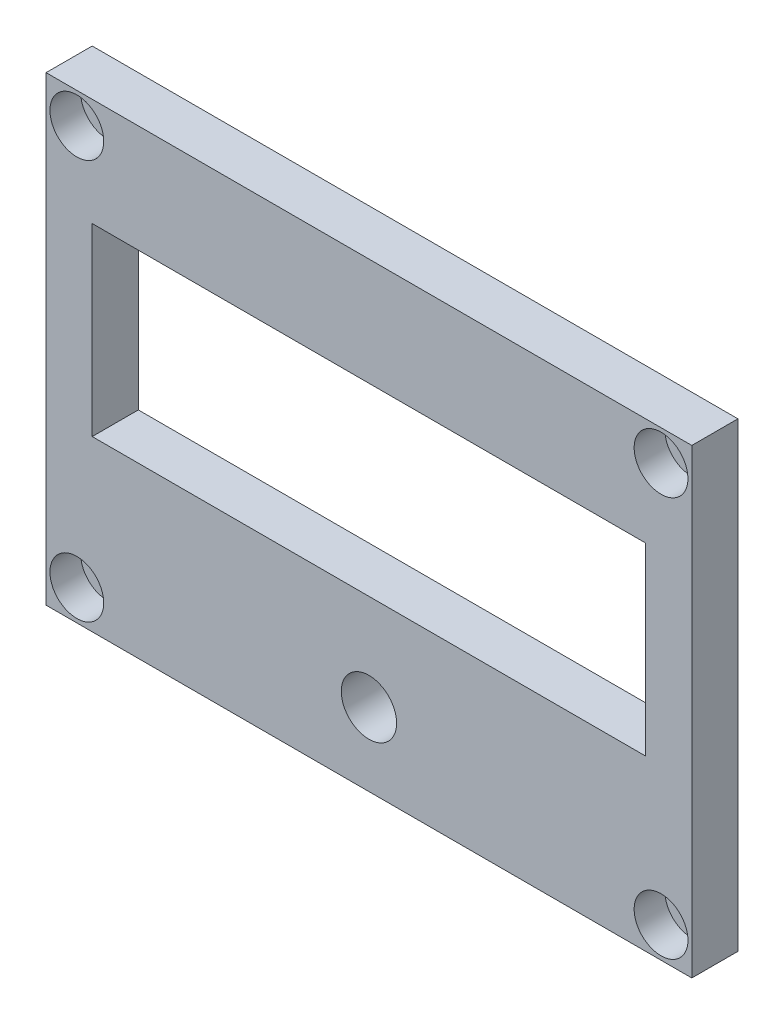
SolidWorks part; units mm, degrees
ref_plane "Front Plane" through (0, 0, 0) normal (0, 0, 1) x (1, 0, 0)
ref_plane "Top Plane" through (0, 0, 0) normal (0, 1, 0) x (1, 0, 0)
ref_plane "Right Plane" through (0, 0, 0) normal (1, 0, 0) x (0, 0, -1)
sketch "Sketch1" plane through (0, 0, 0) normal (0, 0, 1) x (1, 0, 0)
  line L0 (-37, 30) -> (-40, 30)
  line L1 (-37, -30) -> (37, -30)
  line L2 (-40, -27) -> (-40, 27)
  line L3 (-37, 30) -> (37, 30)
  line L4 (44, -27) -> (44, 27)
  line L6 (-37, -30) -> (-40, -30)
  line L7 (-40, 30) -> (-40, 27)
  line L8 (44, -27) -> (44, -30)
  line L9 (37, 30) -> (44, 30)
  line L10 (44, 30) -> (44, 27)
  line L11 (44, -30) -> (37, -30)
  line L12 (-40, -30) -> (-40, -27)
  point P0 (0, 0)
  dimension "D1" = 84
  dimension "D2" = 60
extrude "Boss-Extrude1" add sketch "Sketch1" along normal blind 6
sketch "Sketch3" plane through (0, 0, 6) normal (0, 0, 1) x (1, 0, 0)
  circle A4 centre (-36, 26) radius 3.5
  circle A5 centre (40, 26) radius 3.5
  circle A6 centre (40, -26) radius 3.5
  circle A7 centre (-36, -26) radius 3.5
extrude "Cut-Extrude2" cut sketch "Sketch3" against normal blind 4
sketch "Sketch4" plane through (0, 0, 6) normal (0, 0, 1) x (1, 0, 0)
  circle A0 centre (-36, 26) radius 2
  circle A1 centre (40, 26) radius 2
  circle A2 centre (40, -26) radius 2
  circle A3 centre (-36, -26) radius 2
extrude "Cut-Extrude3" cut sketch "Sketch4" against normal up to surface (6 mm away) up to face at (2, 0, 0)
sketch "Sketch6" plane through (0, 0, 0) normal (0, 0, -1) x (-1, 0, 0)
  line L10 (30.5, -8) -> (-34.5, -8)
  line L14 (-2, 16) -> (-38, 16)
  line L15 (-2, 16) -> (34, 16)
  line L16 (34, 16) -> (34, -8)
  line L17 (34, -8) -> (30.5, -8)
  line L18 (-38, 16) -> (-38, -8)
  line L19 (-38, -8) -> (-34.5, -8)
  circle A3 centre (-2, -20.5) radius 3.6
extrude "Cut-Extrude4" cut sketch "Sketch6" against normal up to surface (6 mm away) up to face at (-39.5, -26, 6)
sketch "Sketch10" plane through (0, 0, 6) normal (0, 0, 1) x (1, 0, 0)
  circle A1 centre (-36, 20) radius 1.5
  circle A2 centre (40, 20) radius 1.5
  circle A3 centre (40, -12) radius 1.5
  circle A4 centre (-36, -12) radius 1.5
extrude "Cut-Extrude6" cut sketch "Sketch10" along normal blind 4 from surface at -6 starting at face at (-1.6, -20.5, 0)
